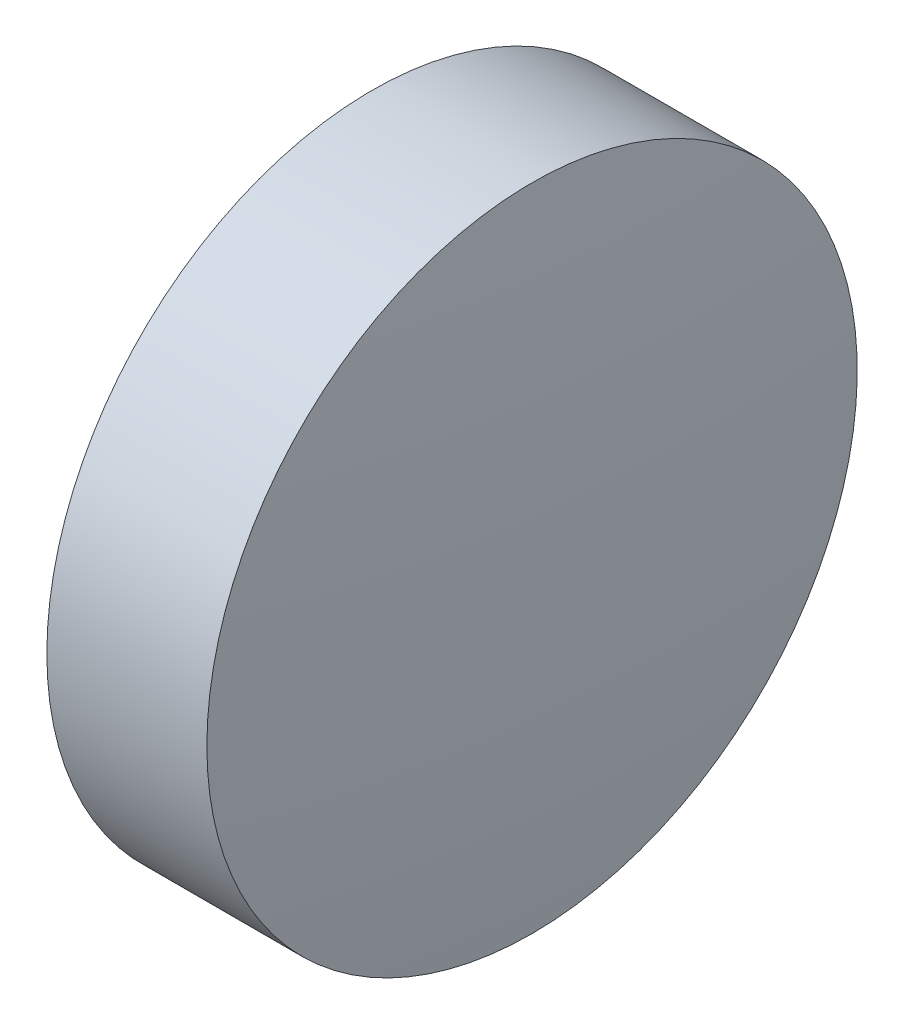
SolidWorks part; units mm, degrees
ref_plane "前视基准面" through (0, 0, 0) normal (0, 0, 1) x (1, 0, 0)
ref_plane "上视基准面" through (0, 0, 0) normal (0, 1, 0) x (1, 0, 0)
ref_plane "右视基准面" through (0, 0, 0) normal (1, 0, 0) x (0, 0, -1)
sketch "草图1" plane through (0, 0, 0) normal (0, 0, 1) x (1, 0, 0)
  line L0 (484.9673, 224.6626) -> (491.1027, 224.6626) construction
  line L1 (485.8289, 224.6626) -> (485.8289, 227.8126)
  line L2 (487.5289, 224.6626) -> (485.8289, 224.6626)
  line L5 (485.8289, 227.8126) -> (487.3789, 227.8126)
  arc A0 (487.5289, 224.6626) -> (487.3789, 227.8126) centre (454.3789, 224.6626) ccw
revolve "旋转1" add sketch "草图1" angle 360 about L0
